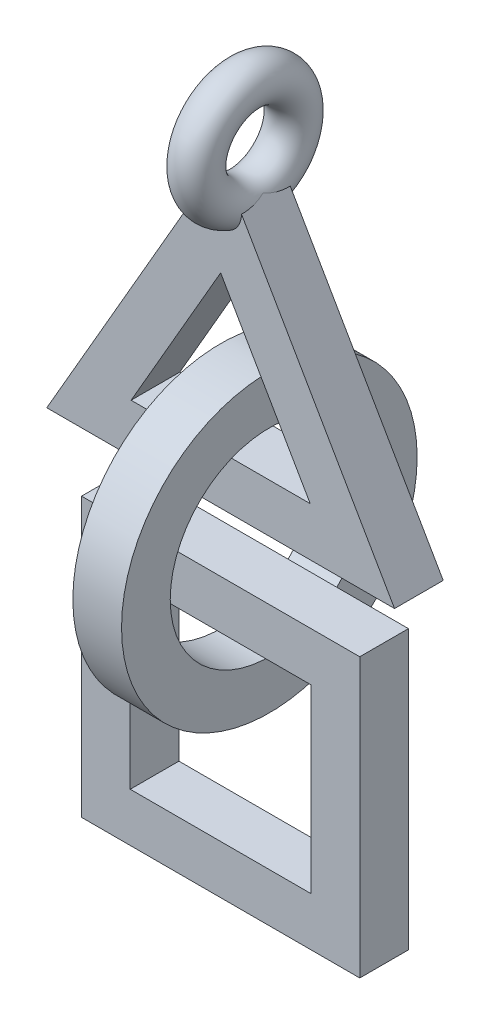
SolidWorks part; units mm, degrees
ref_plane "Front" through (0, 0, 0) normal (0, 0, 1) x (1, 0, 0)
ref_plane "Top" through (0, 0, 0) normal (0, 1, 0) x (1, 0, 0)
ref_plane "Right" through (0, 0, 0) normal (1, 0, 0) x (0, 0, -1)
sketch "Sketch1" plane through (0, 0, 0) normal (0, 0, 1) x (1, 0, 0)
  line L0 (0, 0) -> (-6.35, -10.9985)
  line L1 (-6.35, -10.9985) -> (6.35, -10.9985)
  line L2 (6.35, -10.9985) -> (0, 0)
  line L3 (0, -3.556) -> (-3.2704, -9.2205)
  line L4 (-3.2704, -9.2205) -> (3.2704, -9.2205)
  line L5 (3.2704, -9.2205) -> (0, -3.556)
  dimension "D1" = 12.7
  dimension "D2" = 1.778
extrude "Boss-Extrude1" add sketch "Sketch1" along normal mid plane 1.778
sketch "Sketch2" plane through (0, 0, 0) normal (1, 0, 0) x (0, 0, -1)
  line L0 (-0.889, -9.2205) -> (0.889, -9.2205) construction
  circle A0 centre (0, -12.078) radius 5.3975
  circle A1 centre (0, -12.078) radius 3.6195
  dimension "D2" = 1.778
  dimension "D1" = 10.795
  dimension "D3" = 0.762
extrude "Boss-Extrude2" add sketch "Sketch2" along normal mid plane 1.778 separate body
sketch "Sketch3" plane through (0, 0, 0) normal (0, 0, 1) x (1, 0, 0)
  line L0 (-3.302, -14.9355) -> (3.302, -14.9355)
  line L1 (-5.08, -13.1575) -> (5.08, -13.1575)
  line L2 (-5.08, -13.1575) -> (-5.08, -23.3175)
  line L3 (-5.08, -23.3175) -> (5.08, -23.3175)
  line L4 (5.08, -13.1575) -> (5.08, -23.3175)
  line L5 (3.302, -14.9355) -> (3.302, -21.5395)
  line L6 (-3.302, -21.5395) -> (3.302, -21.5395)
  line L7 (-3.302, -14.9355) -> (-3.302, -21.5395)
  line L8 (0, 0) -> (0, -13.1575) construction
  line L9 (-0.889, -15.6975) -> (0.889, -15.6975) construction
  dimension "D2" = 10.16
  dimension "D4" = 0.762
  dimension "D1" = 1.778
extrude "Boss-Extrude3" add sketch "Sketch3" along normal mid plane 1.778 separate body
sketch "Sketch4" plane through (0, 0, 0) normal (0, 0, 1) x (1, 0, 0)
  line L0 (0, 0.254) -> (1.3174, 0.254) construction
  line L1 (6.35, -10.9985) -> (0, 0) construction
  circle A1 centre (0, -1.524) radius 0.762
  dimension "D1" = 2.032
  dimension "D2" = 1.524
revolve "Revolve1" add sketch "Sketch4" angle 360 about L0
sketch "Sketch5" plane through (0, 0, 0) normal (0, 0, 1) x (1, 0, 0)
  line L1 (-0.7615, -1.3189) -> (-6.35, -10.9985) construction
  line L2 (-0.6599, -1.143) -> (-0.6599, 0.254)
  line L3 (-0.6599, 0.254) -> (0.6599, 0.254)
  line L4 (0.6599, 0.254) -> (0.6599, -1.143)
  line L5 (0.6599, 0.254) -> (0.643, 0.254) construction
  line L6 (0, 0.254) -> (1.3174, 0.254) construction
  circle A1 centre (0, -1.524) radius 0.762
  arc A2 (0.6599, -1.143) -> (-0.6599, -1.143) centre (0, -1.524) ccw
  dimension "D1" = 0
revolve "Cut-Revolve1" cut sketch "Sketch5" angle 360 about L5
sketch "Sketch7" plane through (0, 0, 0) normal (1, 0, 0) x (0, 0, -1)
  line L0 (0, 3.3516) -> (1.9992, 3.3516) construction
  circle A0 centre (0, 0.1766) radius 0.635
  dimension "D1" = 1.27
  dimension "D2" = 6.35
revolve "Revolve3" [suppressed] add sketch "Sketch7" angle 360 about L0
sketch "Sketch6" [suppressed] plane through (0, 0, 0) normal (1, 0, 0) x (0, 0, -1)
  line L0 (-0.0634, 0.889) -> (1.5166, 0.889) construction
  line L1 (-0.889, 0) -> (0.889, 0) construction
  circle A0 centre (0, -0.381) radius 0.635
  dimension "D2" = 1.27
  dimension "D1" = 1.27
  dimension "D3" = 0.254
revolve "Revolve2" [suppressed] add sketch "Sketch6" angle 360 about L0
sketch "Sketch8" plane through (0, 0, 0) normal (0, 1, 0) x (1, 0, 0)
  circle A0 centre (0, 0) radius 0.0013
  dimension "D1" = 0.0025
extrude "Boss-Extrude4" add sketch "Sketch8" against normal up to surface (18.9995 mm away) from offset 2.54 up to face at (0, -21.5395, 0) offset against normal yes
equation "\"Thck\"= .07"
equation "\"D2@Sketch1\"=\"Thck\""
equation "\"D2@Sketch2\"=\"Thck\""
equation "\"D1@Sketch3\"=\"Thck\""
equation "\"D1@Boss-Extrude1\"=\"Thck\""
equation "\"D1@Boss-Extrude2\"=\"Thck\""
equation "\"D1@Boss-Extrude3\"=\"Thck\""
